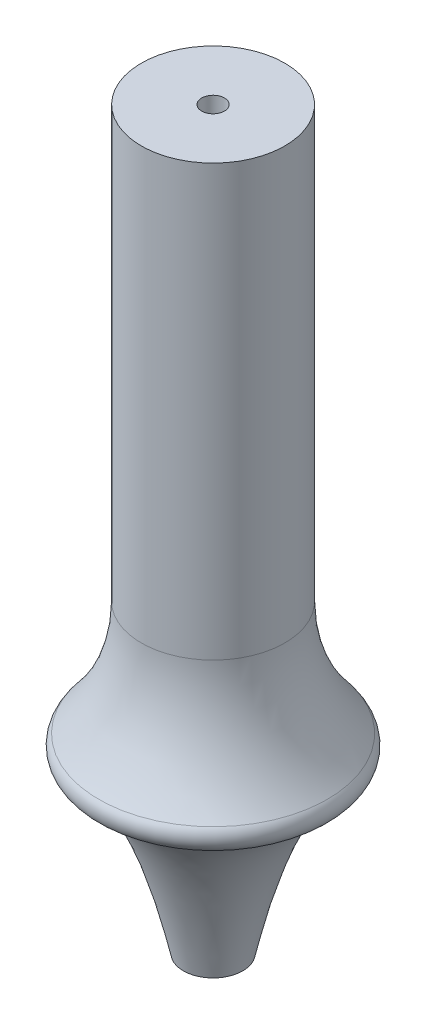
SolidWorks part; units mm, degrees
material "Ceramic Porcelain"
ref_plane "Front Plane" through (0, 0, 0) normal (0, 0, 1) x (1, 0, 0)
ref_plane "Top Plane" through (0, 0, 0) normal (0, 1, 0) x (1, 0, 0)
ref_plane "Right Plane" through (0, 0, 0) normal (1, 0, 0) x (0, 0, -1)
curve "Curve1"
  spline degree 3 poles (0, 0.6058, 14.8325) (0, 0.5941, 14.7866) (0, 0.5772, 14.7202) (0, 0.5557, 14.6369) (0, 0.5416, 14.5846) (0, 0.5291, 14.5387) (0, 0.5168, 14.4961) (0, 0.5048, 14.4554) (0, 0.4926, 14.4157) (0, 0.4802, 14.3766) (0, 0.4673, 14.3378) (0, 0.4538, 14.2991) (0, 0.44, 14.2601) (0, 0.4251, 14.2208) (0, 0.4098, 14.181) (0, 0.3934, 14.1406) (0, 0.3763, 14.0995) (0, 0.3581, 14.0576) (0, 0.3386, 14.015) (0, 0.3182, 13.9713) (0, 0.2963, 13.9267) (0, 0.2734, 13.8809) (0, 0.2489, 13.834) (0, 0.2226, 13.786) (0, 0.1951, 13.7365) (0, 0.1656, 13.6859) (0, 0.1343, 13.6338) (0, 0.1012, 13.5802) (0, 0.0658, 13.5252) (0, 0.0284, 13.4685) (0, -0.0115, 13.4102) (0, -0.0538, 13.3502) (0, -0.0989, 13.2885) (0, -0.1466, 13.2248) (0, -0.1973, 13.1592) (0, -0.2513, 13.0919) (0, -0.3084, 13.0222) (0, -0.3693, 12.9507) (0, -0.4336, 12.8768) (0, -0.5022, 12.8009) (0, -0.5747, 12.7226) (0, -0.6517, 12.6418) (0, -0.7333, 12.5586) (0, -0.8201, 12.473) (0, -0.9119, 12.3846) (0, -1.0094, 12.2937) (0, -1.1128, 12.1999) (0, -1.2223, 12.1032) (0, -1.3386, 12.0037) (0, -1.4617, 11.901) (0, -1.5923, 11.7953) (0, -1.7307, 11.6864) (0, -1.8774, 11.5742) (0, -2.0329, 11.4585) (0, -2.1978, 11.3394) (0, -2.3726, 11.2169) (0, -2.5577, 11.0905) (0, -2.7541, 10.9603) (0, -2.9623, 10.8264) (0, -3.1829, 10.6883) (0, -3.4169, 10.5464) (0, -3.6649, 10.4) (0, -3.9279, 10.2494) (0, -4.207, 10.0945) (0, -4.5028, 9.9348) (0, -4.8167, 9.7706) (0, -5.1498, 9.6017) (0, -5.5033, 9.4277) (0, -5.8785, 9.2488) (0, -6.2768, 9.0646) (0, -6.6999, 8.8753) (0, -7.1493, 8.6805) (0, -7.6269, 8.4801) (0, -8.1346, 8.2742) (0, -8.6743, 8.0622) (0, -9.2486, 7.8445) (0, -9.8597, 7.6204) (0, -10.5102, 7.3901) (0, -11.2033, 7.1535) (0, -11.9418, 6.9102) (0, -12.7294, 6.6604) (0, -13.5696, 6.4035) (0, -14.4667, 6.1396) (0, -15.425, 5.8686) (0, -16.4496, 5.59) (0, -17.5459, 5.3041) (0, -18.7197, 5.0102) (0, -19.9779, 4.7087) (0, -21.3276, 4.399) (0, -22.7771, 4.0809) (0, -24.3355, 3.7545) (0, -26.0129, 3.4195) (0, -27.8206, 3.0755) (0, -29.7714, 2.7227) (0, -31.8798, 2.3605) (0, -34.1622, 1.989) (0, -36.637, 1.6077) (0, -39.3255, 1.2168) (0, -42.252, 0.8158) (0, -45.4444, 0.4033) (0, -47.6661, 0.1383) (0, -48.8258, 0) knots 0 0 0 0 0.002686 0.003888 0.004874 0.005758 0.006588 0.007386 0.008167 0.00894 0.009711 0.010485 0.011266 0.012058 0.012864 0.013686 0.014528 0.01539 0.016276 0.017186 0.018124 0.019091 0.020092 0.021124 0.022194 0.0233 0.024449 0.025638 0.026873 0.028158 0.029491 0.030878 0.032322 0.033824 0.03539 0.037021 0.038721 0.040494 0.042345 0.044277 0.046294 0.048401 0.050602 0.052903 0.055311 0.057829 0.060465 0.063224 0.066114 0.069143 0.072314 0.07564 0.07913 0.082788 0.086628 0.09066 0.094894 0.099341 0.104016 0.10893 0.114098 0.119535 0.125259 0.131285 0.137632 0.144322 0.151373 0.15881 0.166659 0.174943 0.183694 0.19294 0.202718 0.213061 0.224006 0.2356 0.247885 0.26091 0.274732 0.289409 0.305002 0.321583 0.339229 0.358022 0.378056 0.399433 0.422263 0.446671 0.472795 0.500787 0.530818 0.563076 0.597777 0.635159 0.675491 0.719082 0.766278 0.817477 0.873132 0.933772 1 1 1 1
sketch "Sketch2" plane through (0, 0, 0) normal (1, 0, 0) x (0, 0, -1)
  line L0 (-10, 20) -> (-10, 79.984)
  line L1 (-10, 79.984) -> (-1.5875, 79.984)
  line L2 (-1.5875, 79.984) -> (-1.5875, -22.5)
  line L3 (-1.5875, -22.5) -> (-4.143, -22.5)
  line L4 (0, -48.8258) -> (0, 83.4498)
  arc A0 (-15.925, 4.0841) -> (-14.8325, 0.6058) centre (-14.3036, 2.6827) ccw
  arc A2 (-15.925, 4.0841) -> (-10, 20) centre (-34.3392, 20) ccw
  spline S0 degree 3 poles (442.7753, 1947.2807) (-39.7264, -1.3009) (-26.1953, 3.5473) (-14.6369, 0.5557) (-14.5846, 0.5416) (-14.5387, 0.5291) (-14.4961, 0.5168) (-14.4554, 0.5048) (-14.4157, 0.4926) (-14.3766, 0.4802) (-14.3378, 0.4673) (-14.2991, 0.4538) (-14.2601, 0.44) (-14.2208, 0.4251) (-14.181, 0.4098) (-14.1406, 0.3934) (-14.0995, 0.3763) (-14.0576, 0.3581) (-14.015, 0.3386) (-13.9713, 0.3182) (-13.9267, 0.2963) (-13.8809, 0.2734) (-13.834, 0.2489) (-13.786, 0.2226) (-13.7365, 0.1951) (-13.6859, 0.1656) (-13.6338, 0.1343) (-13.5802, 0.1012) (-13.5252, 0.0658) (-13.4685, 0.0284) (-13.4102, -0.0115) (-13.3502, -0.0538) (-13.2885, -0.0989) (-13.2248, -0.1466) (-13.1592, -0.1973) (-13.0919, -0.2513) (-13.0222, -0.3084) (-12.9507, -0.3693) (-12.8768, -0.4336) (-12.8009, -0.5022) (-12.7226, -0.5747) (-12.6418, -0.6517) (-12.5586, -0.7333) (-12.473, -0.8201) (-12.3846, -0.9119) (-12.2937, -1.0094) (-12.1999, -1.1128) (-12.1032, -1.2223) (-12.0037, -1.3386) (-11.901, -1.4617) (-11.7953, -1.5923) (-11.6864, -1.7307) (-11.5742, -1.8774) (-11.4585, -2.0329) (-11.3394, -2.1978) (-11.2169, -2.3726) (-11.0905, -2.5577) (-10.9603, -2.7541) (-10.8264, -2.9623) (-10.6883, -3.1829) (-10.5464, -3.4169) (-10.4, -3.6649) (-10.2494, -3.9279) (-10.0945, -4.207) (-9.9348, -4.5028) (-9.7706, -4.8167) (-9.6017, -5.1498) (-9.4277, -5.5033) (-9.2488, -5.8785) (-9.0646, -6.2768) (-8.8753, -6.6999) (-8.6805, -7.1493) (-8.4801, -7.6269) (-8.2742, -8.1346) (-8.0622, -8.6743) (-7.8445, -9.2486) (-7.6204, -9.8597) (-7.3901, -10.5102) (-7.1535, -11.2033) (-6.9102, -11.9418) (-6.6604, -12.7294) (-6.4035, -13.5696) (-6.1396, -14.4667) (-5.8686, -15.425) (-5.59, -16.4496) (-5.3041, -17.5459) (-5.0102, -18.7197) (-4.7087, -19.9779) (-4.399, -21.3276) (-4.0809, -22.7771) (-3.7545, -24.3355) (-3.4195, -26.0129) (-3.0755, -27.8206) (-2.7227, -29.7714) (-2.3605, -31.8798) (-1.989, -34.1622) (-1.6077, -36.637) (-1.2168, -39.3255) (-0.8158, -42.252) (9.9601, -125.6496) (-9.3783, -211.767) (1994.8812, -47.5876) knots -0.672122 -0.672122 -0.672122 -0.672122 0.002686 0.003888 0.004874 0.005758 0.006588 0.007386 0.008167 0.00894 0.009711 0.010485 0.011266 0.012058 0.012864 0.013686 0.014528 0.01539 0.016276 0.017186 0.018124 0.019091 0.020092 0.021124 0.022194 0.0233 0.024449 0.025638 0.026873 0.028158 0.029491 0.030878 0.032322 0.033824 0.03539 0.037021 0.038721 0.040494 0.042345 0.044277 0.046294 0.048401 0.050602 0.052903 0.055311 0.057829 0.060465 0.063224 0.066114 0.069143 0.072314 0.07564 0.07913 0.082788 0.086628 0.09066 0.094894 0.099341 0.104016 0.10893 0.114098 0.119535 0.125259 0.131285 0.137632 0.144322 0.151373 0.15881 0.166659 0.174943 0.183694 0.19294 0.202718 0.213061 0.224006 0.2356 0.247885 0.26091 0.274732 0.289409 0.305002 0.321583 0.339229 0.358022 0.378056 0.399433 0.422263 0.446671 0.472795 0.500787 0.530818 0.563076 0.597777 0.635159 0.675491 0.719082 0.766278 0.817477 0.873132 0.933772 5.58568 5.58568 5.58568 5.58568 only from (-14.8325, 0.6058) to (0, -48.8258) construction
  spline S1 degree 3 poles (-14.8325, 0.6058) (-14.7866, 0.5941) (-14.7202, 0.5772) (-14.6369, 0.5557) (-14.5846, 0.5416) (-14.5387, 0.5291) (-14.4961, 0.5168) (-14.4554, 0.5048) (-14.4157, 0.4926) (-14.3766, 0.4802) (-14.3378, 0.4673) (-14.2991, 0.4538) (-14.2601, 0.44) (-14.2208, 0.4251) (-14.181, 0.4098) (-14.1406, 0.3934) (-14.0995, 0.3763) (-14.0576, 0.3581) (-14.015, 0.3386) (-13.9713, 0.3182) (-13.9267, 0.2963) (-13.8809, 0.2734) (-13.834, 0.2489) (-13.786, 0.2226) (-13.7365, 0.1951) (-13.6859, 0.1656) (-13.6338, 0.1343) (-13.5802, 0.1012) (-13.5252, 0.0658) (-13.4685, 0.0284) (-13.4102, -0.0115) (-13.3502, -0.0538) (-13.2885, -0.0989) (-13.2248, -0.1466) (-13.1592, -0.1973) (-13.0919, -0.2513) (-13.0222, -0.3084) (-12.9507, -0.3693) (-12.8768, -0.4336) (-12.8009, -0.5022) (-12.7226, -0.5747) (-12.6418, -0.6517) (-12.5586, -0.7333) (-12.473, -0.8201) (-12.3846, -0.9119) (-12.2937, -1.0094) (-12.1999, -1.1128) (-12.1032, -1.2223) (-12.0037, -1.3386) (-11.901, -1.4617) (-11.7953, -1.5923) (-11.6864, -1.7307) (-11.5742, -1.8774) (-11.4585, -2.0329) (-11.3394, -2.1978) (-11.2169, -2.3726) (-11.0905, -2.5577) (-10.9603, -2.7541) (-10.8264, -2.9623) (-10.6883, -3.1829) (-10.5464, -3.4169) (-10.4, -3.6649) (-10.2494, -3.9279) (-10.0945, -4.207) (-9.9348, -4.5028) (-9.7706, -4.8167) (-9.6017, -5.1498) (-9.4277, -5.5033) (-9.2488, -5.8785) (-9.0646, -6.2768) (-8.8753, -6.6999) (-8.6805, -7.1493) (-8.4801, -7.6269) (-8.2742, -8.1346) (-8.0622, -8.6743) (-7.8445, -9.2486) (-7.6204, -9.8597) (-7.3901, -10.5102) (-7.1535, -11.2033) (-6.9102, -11.9418) (-6.6604, -12.7294) (-6.4035, -13.5696) (-6.1396, -14.4667) (-5.8686, -15.425) (-5.59, -16.4496) (-5.3041, -17.5459) (-5.0102, -18.7197) (-4.7087, -19.9779) (-4.399, -21.3276) (-4.0809, -22.7771) (-3.7545, -24.3355) (-3.4195, -26.0129) (-3.0755, -27.8206) (-2.7227, -29.7714) (-2.3605, -31.8798) (-1.989, -34.1622) (-1.6077, -36.637) (-1.2168, -39.3255) (-0.8158, -42.252) (-0.4033, -45.4444) (-0.1383, -47.6661) (0, -48.8258) knots 0 0 0 0 0.002686 0.003888 0.004874 0.005758 0.006588 0.007386 0.008167 0.00894 0.009711 0.010485 0.011266 0.012058 0.012864 0.013686 0.014528 0.01539 0.016276 0.017186 0.018124 0.019091 0.020092 0.021124 0.022194 0.0233 0.024449 0.025638 0.026873 0.028158 0.029491 0.030878 0.032322 0.033824 0.03539 0.037021 0.038721 0.040494 0.042345 0.044277 0.046294 0.048401 0.050602 0.052903 0.055311 0.057829 0.060465 0.063224 0.066114 0.069143 0.072314 0.07564 0.07913 0.082788 0.086628 0.09066 0.094894 0.099341 0.104016 0.10893 0.114098 0.119535 0.125259 0.131285 0.137632 0.144322 0.151373 0.15881 0.166659 0.174943 0.183694 0.19294 0.202718 0.213061 0.224006 0.2356 0.247885 0.26091 0.274732 0.289409 0.305002 0.321583 0.339229 0.358022 0.378056 0.399433 0.422263 0.446671 0.472795 0.500787 0.530818 0.563076 0.597777 0.635159 0.675491 0.719082 0.766278 0.817477 0.873132 0.933772 1 1 1 1
  dimension "D3" = 59.984
  dimension "D1" = 20
  dimension "D2" = 10
  dimension "D4" = 22.5
  dimension "D5" = 1.5875
revolve "Revolve1" add sketch "Sketch2" angle 360 about L4
equation "\"r_cc_inner\"= 10'combustion chamber inner radius [mm]"
equation "\"r_cc_outer\"= 24'combustion chamber outer radius [mm]"
equation "\"L_star\"= 1500'combustion process characteristic length [mm]"
equation "\"At\"= 0.0000598 * ( 1000 ) ^ 2'Throat Area [mm^2]"
equation "\"x_cc\"= \"L_star\" * \"At\" / ( pi * ( \"r_cc_outer\" ^ 2 - \"r_cc_inner\" ^ 2 ) )'combustion chamber physical length [mm]"
equation "\"x_convergent\"= 20'length of the convergent section of the nozzle [mm]"
equation "\"r_throat\"= 15'outer radius of throat gap [mm]"
equation "\"x_material_change\"= 1.5 * \"r_throat\"'distance below throat at which nozzle material changes to a low-temp material [mm]"
equation "\"t_i\"= 8'insulation thickness required by thermal considerations [mm]"
equation "\"t_cw\"= 4'pressure vessle cylinder wall thickness required by structural considerations [mm]"
equation "\"t_p\" = 1 / 4 * 25.4'pressure vessle plate thickness required by structural considerations [mm]"
equation "\"r_outer\"= \"r_cc_outer\" + \"t_i\" + \"t_cw\" + 10'overall outermost radius of engine [mm]"
equation "\"D1@Sketch2\"=\"x_convergent\""
equation "\"D2@Sketch2\"=\"r_cc_inner\""
equation "\"D3@Sketch2\"=\"x_cc\""
equation "\"r_rod\"= 1 / 8 * 25.4 / 2'radius of the threaded rod in the center fo the spike [mm]"
equation "\"D4@Sketch2\"=\"x_material_change\""
equation "\"D5@Sketch2\" = \"r_rod\""
